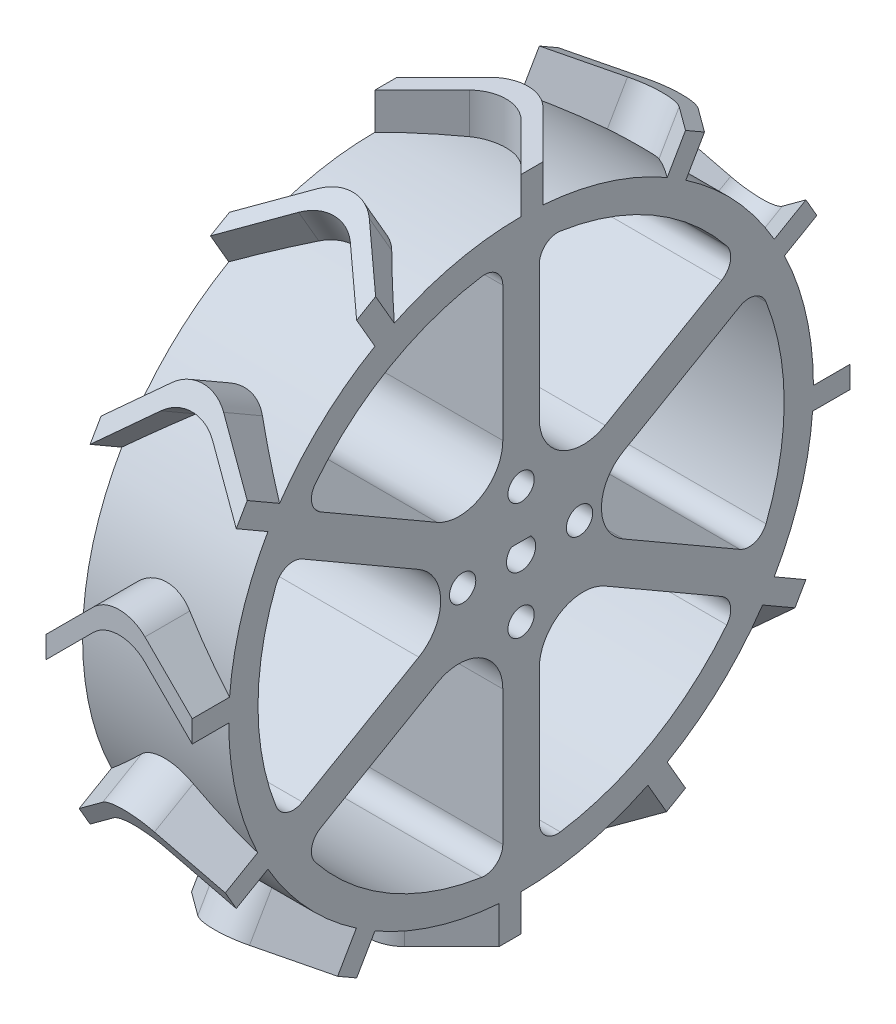
SolidWorks part; units mm, degrees
material "PLA 15%"
ref_plane "Front Plane" through (0, 0, 0) normal (0, 0, 1) x (1, 0, 0)
ref_plane "Top Plane" through (0, 0, 0) normal (0, 1, 0) x (1, 0, 0)
ref_plane "Right Plane" through (0, 0, 0) normal (1, 0, 0) x (0, 0, -1)
sketch "Sketch2" plane through (0, 0, 0) normal (1, 0, 0) x (0, 0, -1)
  circle A2 centre (0, 0) radius 40
  dimension "D1" = 80
extrude "Boss-Extrude1" add sketch "Sketch2" along normal blind 20
sketch "Sketch4" plane through (0, 0, 0) normal (0, 1, 0) x (1, 0, 0)
  line L8 (0, 0) -> (20, 0) construction
  line L9 (20, -40) -> (20, 40) construction
  line L10 (0, 0) -> (6.4645, 6.4645)
  line L11 (13.5355, 6.4645) -> (20, 0)
  line L12 (20, 0) -> (20, 3)
  line L13 (20, 3) -> (13.5355, 9.4645)
  line L14 (6.4645, 9.4645) -> (0, 3)
  line L15 (0, 40) -> (0, -40) construction
  line L16 (0, 3) -> (0, 0)
  arc A0 (13.5355, 9.4645) -> (6.4645, 9.4645) centre (10, 5.9289) ccw
  arc A1 (6.4645, 6.4645) -> (13.5355, 6.4645) centre (10, 2.9289) cw
  point P4 (10, 0)
  point P18 (10, 13)
  point P21 (10, 10)
  dimension "D3" = 5
  dimension "D1" = 3
  dimension "D2" = 3
  dimension "D4" = 10
extrude "Boss-Extrude2" add sketch "Sketch4" along normal blind 45
pattern_circular "CirPattern2" count 12 over 360 about axis through (0, 0, 0) along (1, 0, 0) of "Boss-Extrude2"
sketch "Sketch5" plane through (0, 0, 0) normal (-1, 0, 0) x (0, 0, 1)
  line L0 (0, 0) -> (0, 40) construction
  line L1 (0, 0) -> (34.641, 20) construction
  line L6 (2.5, 33.1248) -> (2.5, 4.3301)
  line L8 (27.4369, 18.7274) -> (2.5, 4.3301)
  circle A0 centre (0, 0) radius 40 construction
  arc A2 (5.3731, 35.5968) -> (28.1411, 22.4517) centre (0, 0) cw
  arc A6 (28.1411, 22.4517) -> (27.4369, 18.7274) centre (26.1869, 20.8925) cw
  arc A7 (5.3731, 35.5968) -> (2.5, 33.1248) centre (5, 33.1248) ccw
  circle A10 centre (0, 0) radius 40 construction
  point P11 (0, 35.9131)
  point P22 (2.5, 35.9131)
  dimension "D1" = 2.5
  dimension "D2" = 4
  dimension "D8" = 2.5
  dimension "D7" = 2.5
  dimension "D9" = 60
extrude "Cut-Extrude3" cut sketch "Sketch5" against normal up to next (20 mm away)
fillet "Fillet1" radius 6 1 edges at (10, 4.3301, 2.5)
pattern_circular "CirPattern3" count 6 over 360 about axis through (0, 0, 0) along (1, 0, 0) of "Cut-Extrude3", "Fillet1"
sketch "Sketch6" plane through (0, 0, 0) normal (-1, 0, 0) x (0, 0, 1)
  circle A0 centre (0, 8) radius 1.8
  circle A1 centre (8, 0) radius 1.8
  circle A2 centre (0, -8) radius 1.8
  circle A3 centre (-8, 0) radius 1.8
  point P0 (0, 0)
  point P13 (0, 0)
  dimension "D1" = 3.6
  dimension "D2" = 8
  dimension "D3" = 4
extrude "Cut-Extrude4" cut sketch "Sketch6" against normal up to next
sketch "Sketch8" plane through (0, 0, 0) normal (1, 0, 0) x (0, 0, -1)
  line L0 (1.3229, 1.5) -> (-1.3229, 1.5)
  arc A0 (1.3229, 1.5) -> (-1.3229, 1.5) centre (0, 0) cw
  point P4 (0, -2)
  dimension "D1" = 2
  dimension "D2" = 3.5
extrude "Cut-Extrude6" cut sketch "Sketch8" along normal through all both and the other way through all contours A0 L0
